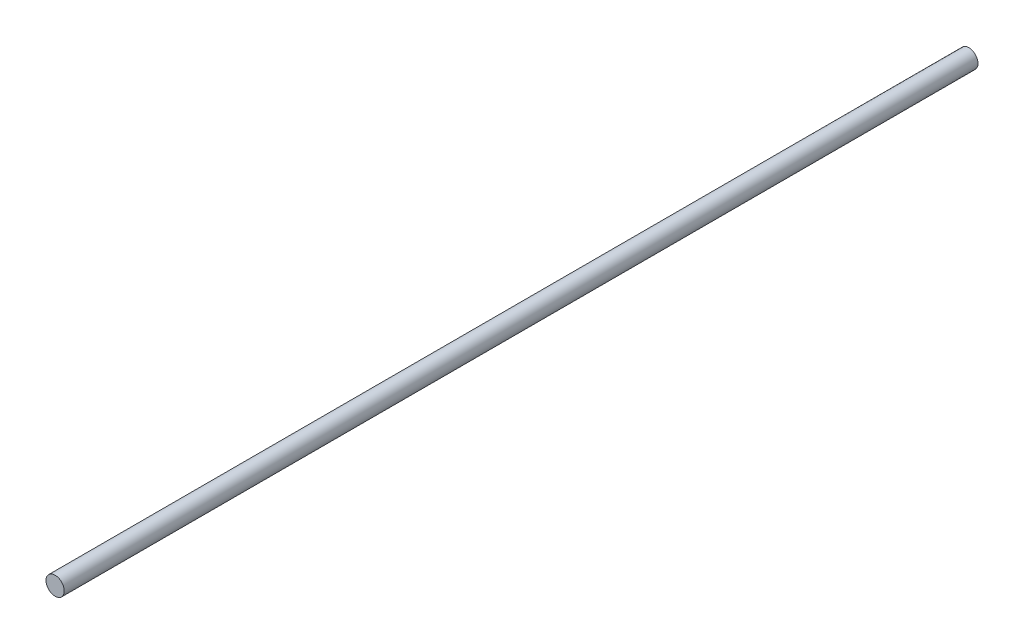
SolidWorks part; units mm, degrees
ref_plane "前视基准面" through (0, 0, 0) normal (0, 0, 1) x (1, 0, 0)
ref_plane "上视基准面" through (0, 0, 0) normal (0, 1, 0) x (1, 0, 0)
ref_plane "右视基准面" through (0, 0, 0) normal (1, 0, 0) x (0, 0, -1)
sketch "草图2" plane through (0, 0, 0) normal (0, 0, 1) x (1, 0, 0)
  circle A0 centre (0, 0) radius 2
extrude "凸台-拉伸1" add sketch "草图2" along normal blind 200
